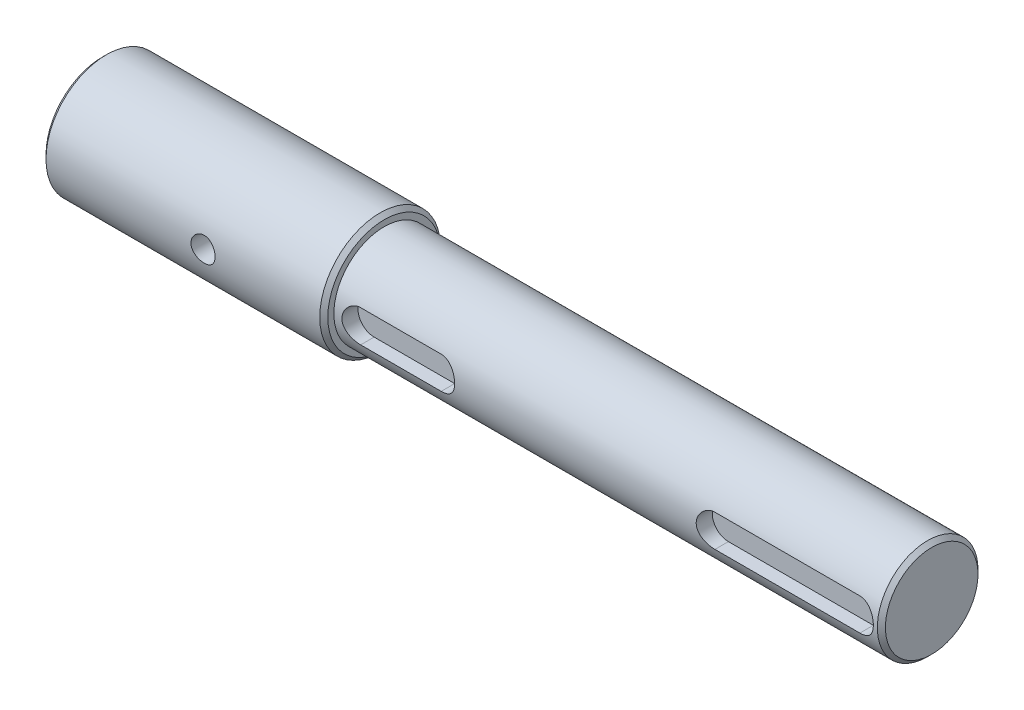
SolidWorks part; units mm, degrees
material "AISI 1045 钢，冷拔"
ref_plane "前视基准面" through (0, 0, 0) normal (0, 0, 1) x (1, 0, 0)
ref_plane "上视基准面" through (0, 0, 0) normal (0, 1, 0) x (1, 0, 0)
ref_plane "右视基准面" through (0, 0, 0) normal (1, 0, 0) x (0, 0, -1)
sketch "草图1" plane through (0, 0, 0) normal (1, 0, 0) x (0, 0, -1)
  circle A0 centre (0, 0) radius 12.5
  dimension "D1" = 25
extrude "凸台-拉伸1" add sketch "草图1" along normal blind 136
sketch "草图2" plane through (0, 0, 0) normal (-1, 0, 0) x (0, 0, 1)
  circle A0 centre (0, 0) radius 15
  dimension "D1" = 30
extrude "凸台-拉伸2" add sketch "草图2" along normal blind 70
chamfer "倒角1" distance 1 angle 45 3 edges at (136, 0, -12.5) (0, 0, 15) (-70, 0, 15)
ref_plane "基准面1" through (0, 0, 12.5) normal (0, 0, 1) x (1, 0, 0)
sketch "草图3" plane through (0, 0, 12.5) normal (0, 0, 1) x (1, 0, 0)
  line L0 (0, 0) -> (136, 0) construction
  line L1 (136, -11.5) -> (136, 11.5) construction
  line L2 (6, 4) -> (26, 4)
  line L3 (6, -4) -> (26, -4)
  line L4 (94, 4) -> (130, 4)
  line L5 (0, 4) -> (136, 4) construction
  line L6 (0, -4) -> (136, -4) construction
  line L7 (94, -4) -> (130, -4)
  arc A0 (130, -4) -> (130, 4) centre (130, 0) ccw
  arc A1 (94, 4) -> (94, -4) centre (94, 0) ccw
  arc A2 (26, -4) -> (26, 4) centre (26, 0) ccw
  arc A3 (6, 4) -> (6, -4) centre (6, 0) ccw
  dimension "D3" = 36
  dimension "D1" = 4
  dimension "D4" = 20
  dimension "D5" = 68
  dimension "D6" = 6
  dimension "D2" = 4
extrude "切除-拉伸1" cut sketch "草图3" against normal blind 4
sketch "草图4" plane through (0, 0, 0) normal (0, 0, 1) x (1, 0, 0)
  line L0 (15.0818, 0) -> (-63.4871, 0) construction
  line L1 (-70, 14) -> (-70, -14) construction
  circle A0 centre (-30, 0) radius 3
  dimension "D1" = 6
  dimension "D2" = 40
extrude "切除-拉伸2" cut sketch "草图4" against normal through all both and the other way through all
